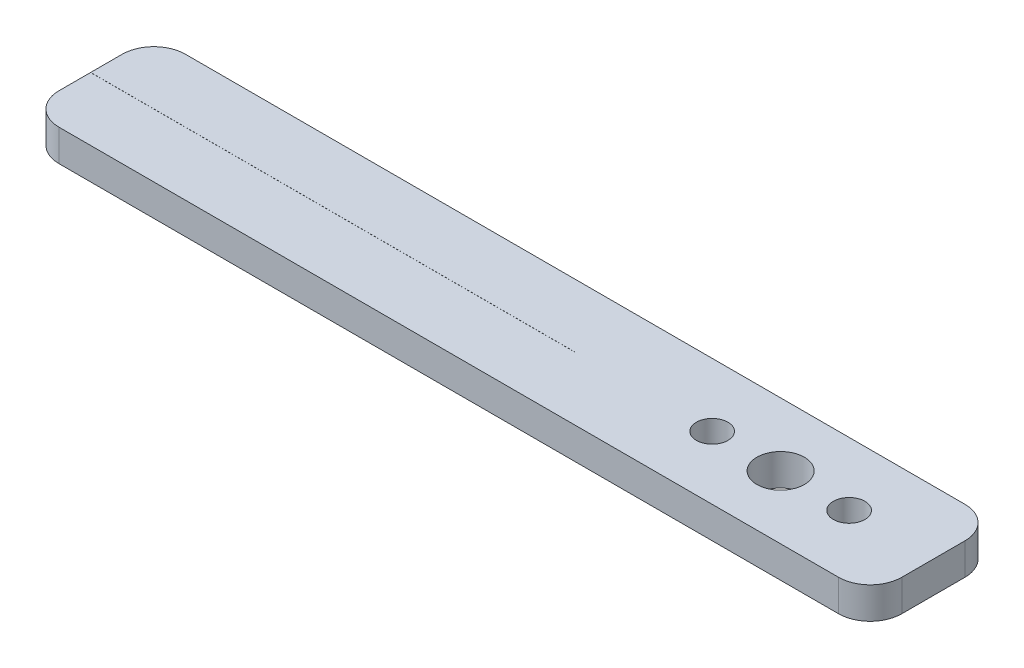
SolidWorks part; units mm, degrees
ref_plane "Front Plane" through (0, 0, 0) normal (0, 0, 1) x (1, 0, 0)
ref_plane "Top Plane" through (0, 0, 0) normal (0, 1, 0) x (1, 0, 0)
ref_plane "Right Plane" through (0, 0, 0) normal (1, 0, 0) x (0, 0, -1)
sketch "Sketch1" plane through (0, 0, 0) normal (0, 1, 0) x (1, 0, 0)
  line L1 (-37, 4) -> (37, 4)
  line L2 (-40, 1) -> (-40, -5)
  line L3 (-37, -8) -> (37, -8)
  line L4 (40, 1) -> (40, -5)
  arc A0 (-37, 4) -> (-40, 1) centre (-37, 1) ccw
  arc A1 (-40, -5) -> (-37, -8) centre (-37, -5) ccw
  arc A2 (37, 4) -> (40, 1) centre (37, 1) cw
  arc A3 (37, -8) -> (40, -5) centre (37, -5) ccw
  point P0 (0, 0)
  point P8 (-40, 4)
  point P13 (40, 4)
  point P16 (40, -8)
  dimension "D3" = 3
  dimension "D1" = 12
  dimension "D2" = 80
extrude "Boss-Extrude1" add sketch "Sketch1" along normal blind 3 contours L1 A2 L4 A3 L3 A1 L2 A0
sketch "Sketch2" plane through (0, 3, 0) normal (0, 1, 0) x (1, 0, 0)
  line L0 (25.5, 4) -> (25.5, -8) construction
  line L1 (-37, 4) -> (37, 4) construction
  line L2 (-37, -8) -> (37, -8) construction
  line L3 (-40, 1) -> (-40, -5) construction
  line L4 (-40, -2.005) -> (5.9526, -2.005)
  line L5 (-40, -2.005) -> (-40, -1.995)
  line L6 (-40, -1.995) -> (5.9526, -1.995)
  line L7 (5.9526, -2.005) -> (5.9526, -1.995)
  line L8 (-40, -2.005) -> (5.9526, -1.995) construction
  line L9 (-40, -1.995) -> (5.9526, -2.005) construction
  line L10 (40, 1) -> (40, -5) construction
  circle A0 centre (32, -2) radius 1.5
  circle A1 centre (25.5, -2) radius 2.25
  circle A2 centre (19, -2) radius 1.5
  point P16 (-17.0237, -2)
  point P19 (0, 0)
  point P22 (40, -2)
  dimension "D1" = 3
  dimension "D2" = 4.5
  dimension "D3" = 6.5
  dimension "D4" = 0.01
  dimension "D5" = 8
extrude "Cut-Extrude1" cut sketch "Sketch2" against normal through all
